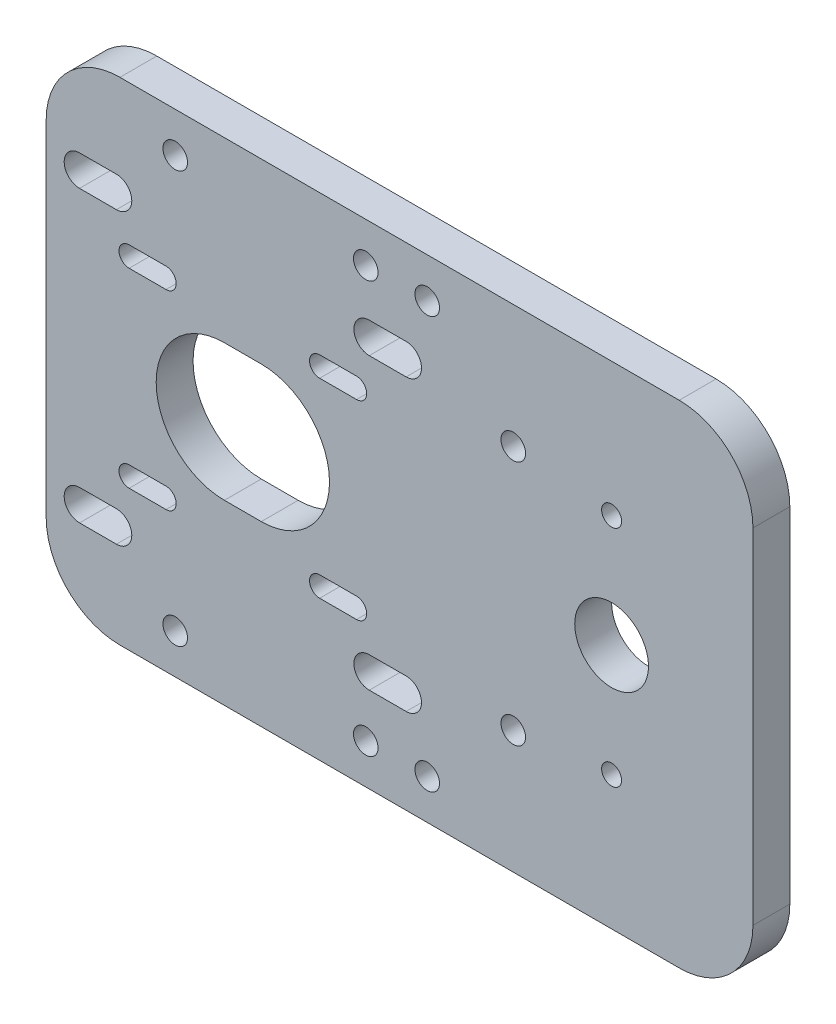
SolidWorks part; units mm, degrees
ref_plane "Alzado" through (0, 0, 0) normal (0, 0, 1) x (1, 0, 0)
ref_plane "Planta" through (0, 0, 0) normal (0, 1, 0) x (1, 0, 0)
ref_plane "Vista lateral" through (0, 0, 0) normal (1, 0, 0) x (0, 0, -1)
sketch "Croquis1" plane through (0, 0, 0) normal (0, 0, 1) x (1, 0, 0)
  line L1 (0, 0) -> (115, 0)
  line L2 (0, 0) -> (0, 80)
  line L3 (0, 80) -> (115, 80)
  line L4 (115, 0) -> (115, 80)
  dimension "D1" = 80
  dimension "D2" = 115
extrude "Saliente-Extruir1" add sketch "Croquis1" along normal blind 6
sketch "Croquis2" plane through (0, 0, 0) normal (0, 0, -1) x (-1, 0, 0)
  line L0 (0, 80) -> (0, 0) construction
  line L1 (0, 40) -> (-115, 40) construction
  line L4 (-115, 0) -> (-115, 80) construction
  line L7 (-29, 40) -> (-35, 40) construction
  line L10 (-29, 28.9) -> (-35, 28.9)
  line L19 (-29, 51.1) -> (-35, 51.1)
  line L20 (-13.5, 24.5) -> (-19.5, 24.5) construction
  line L21 (-13.5, 22.85) -> (-19.5, 22.85)
  line L22 (-13.5, 26.15) -> (-19.5, 26.15)
  line L23 (-44.5, 55.5) -> (-50.5, 55.5) construction
  line L24 (-44.5, 53.85) -> (-50.5, 53.85)
  line L25 (-44.5, 57.15) -> (-50.5, 57.15)
  line L26 (-44.5, 24.5) -> (-50.5, 24.5) construction
  line L27 (-44.5, 22.85) -> (-50.5, 22.85)
  line L28 (-44.5, 26.15) -> (-50.5, 26.15)
  line L29 (-13.5, 55.5) -> (-19.5, 55.5) construction
  line L30 (-13.5, 53.85) -> (-19.5, 53.85)
  line L31 (-13.5, 57.15) -> (-19.5, 57.15)
  line L32 (-92, 0) -> (-92, 80) construction
  line L33 (0, 0) -> (-115, 0) construction
  line L34 (-115, 80) -> (0, 80) construction
  line L35 (-61, 0) -> (-61, 80) construction
  line L36 (-52.57, 16.43) -> (-58.57, 16.43) construction
  line L37 (-52.57, 13.93) -> (-58.57, 13.93)
  line L38 (-52.57, 18.93) -> (-58.57, 18.93)
  line L39 (-5.43, 16.43) -> (-11.43, 16.43) construction
  line L40 (-5.43, 13.93) -> (-11.43, 13.93)
  line L41 (-5.43, 18.93) -> (-11.43, 18.93)
  line L42 (-52.57, 63.57) -> (-58.57, 63.57) construction
  line L43 (-52.57, 61.07) -> (-58.57, 61.07)
  line L44 (-52.57, 66.07) -> (-58.57, 66.07)
  line L45 (-5.43, 63.57) -> (-11.43, 63.57) construction
  line L46 (-5.43, 61.07) -> (-11.43, 61.07)
  line L47 (-5.43, 66.07) -> (-11.43, 66.07)
  circle A5 centre (-92, 40) radius 6
  circle A15 centre (-92, 21.75) radius 1.625
  circle A16 centre (-92, 58.25) radius 1.625
  arc A19 (-29, 28.9) -> (-29, 51.1) centre (-29, 40) ccw
  arc A20 (-35, 51.1) -> (-35, 28.9) centre (-35, 40) ccw
  arc A21 (-13.5, 22.85) -> (-13.5, 26.15) centre (-13.5, 24.5) ccw
  arc A22 (-19.5, 26.15) -> (-19.5, 22.85) centre (-19.5, 24.5) ccw
  arc A23 (-44.5, 53.85) -> (-44.5, 57.15) centre (-44.5, 55.5) ccw
  arc A24 (-50.5, 57.15) -> (-50.5, 53.85) centre (-50.5, 55.5) ccw
  arc A25 (-44.5, 22.85) -> (-44.5, 26.15) centre (-44.5, 24.5) ccw
  arc A26 (-50.5, 26.15) -> (-50.5, 22.85) centre (-50.5, 24.5) ccw
  arc A27 (-13.5, 53.85) -> (-13.5, 57.15) centre (-13.5, 55.5) ccw
  arc A28 (-19.5, 57.15) -> (-19.5, 53.85) centre (-19.5, 55.5) ccw
  arc A29 (-52.57, 13.93) -> (-52.57, 18.93) centre (-52.57, 16.43) ccw
  arc A30 (-58.57, 18.93) -> (-58.57, 13.93) centre (-58.57, 16.43) ccw
  arc A31 (-5.43, 13.93) -> (-5.43, 18.93) centre (-5.43, 16.43) ccw
  arc A32 (-11.43, 18.93) -> (-11.43, 13.93) centre (-11.43, 16.43) ccw
  arc A33 (-52.57, 61.07) -> (-52.57, 66.07) centre (-52.57, 63.57) ccw
  arc A34 (-58.57, 66.07) -> (-58.57, 61.07) centre (-58.57, 63.57) ccw
  arc A35 (-5.43, 61.07) -> (-5.43, 66.07) centre (-5.43, 63.57) ccw
  arc A36 (-11.43, 66.07) -> (-11.43, 61.07) centre (-11.43, 63.57) ccw
  circle A37 centre (-76, 20) radius 2
  circle A38 centre (-76, 60) radius 2
  point P6 (-32, 40)
  point P19 (-16.5, 24.5)
  point P28 (-47.5, 55.5)
  point P35 (-47.5, 24.5)
  point P41 (-55.57, 16.43)
  point P48 (-16.5, 55.5)
  point P63 (-8.43, 16.43)
  point P72 (-55.57, 63.57)
  point P79 (-8.43, 63.57)
  dimension "D2" = 6
  dimension "D3" = 11.1
  dimension "D4" = 3.3
  dimension "D5" = 6
  dimension "D6" = 12
  dimension "D13" = 3.25
  dimension "D14" = 3.25
  dimension "D29" = 2.5
  dimension "D32" = 2.5
  dimension "D34" = 2.5
  dimension "D36" = 2.5
  dimension "D45" = 4
  dimension "D46" = 4
  dimension "D7" = 15.5
  dimension "D8" = 15.5
  dimension "D9" = 3.3
  dimension "D10" = 6
  dimension "D11" = 23
  dimension "D12" = 40
  dimension "D15" = 18.25
  dimension "D16" = 18.25
  dimension "D17" = 3.3
  dimension "D18" = 6
  dimension "D19" = 3.3
  dimension "D20" = 6
  dimension "D21" = 15.5
  dimension "D22" = 15.5
  dimension "D23" = 15.5
  dimension "D24" = 15.5
  dimension "D25" = 15.5
  dimension "D26" = 15.5
  dimension "D27" = 60
  dimension "D28" = 26
  dimension "D30" = 6
  dimension "D31" = 6
  dimension "D33" = 6
  dimension "D35" = 6
  dimension "D37" = 23.57
  dimension "D38" = 23.57
  dimension "D39" = 23.57
  dimension "D40" = 23.57
  dimension "D41" = 23.57
  dimension "D42" = 23.57
  dimension "D43" = 23.57
  dimension "D44" = 23.57
  dimension "D47" = 20
  dimension "D48" = 39
  dimension "D49" = 39
  dimension "D50" = 20
extrude "Cortar-Extruir1" cut sketch "Croquis2" against normal through all
fillet "Redondeo1" radius 12 4 edges at (115, 0, 3) (115, 80, 3) (0, 0, 3) (0, 80, 3)
sketch "Croquis3" plane through (0, 0, 0) normal (0, 0, -1) x (-1, 0, 0)
  line L0 (-12, 0) -> (-103, 0) construction
  line L1 (0, 68) -> (0, 12) construction
  line L2 (-103, 80) -> (-12, 80) construction
  circle A0 centre (-21, 6.5) radius 2
  circle A1 centre (-62, 6.5) radius 2
  circle A2 centre (-62, 73.5) radius 2
  circle A3 centre (-21, 73.5) radius 2
  circle A4 centre (-52, 6.5) radius 2
  circle A5 centre (-52, 73.5) radius 2
  dimension "D1" = 4
  dimension "D2" = 4
  dimension "D3" = 4
  dimension "D4" = 4
  dimension "D13" = 4
  dimension "D14" = 4
  dimension "D5" = 6.5
  dimension "D6" = 6.5
  dimension "D7" = 21
  dimension "D8" = 62
  dimension "D9" = 6.5
  dimension "D10" = 6.5
  dimension "D11" = 21
  dimension "D12" = 62
  dimension "D15" = 6.5
  dimension "D16" = 6.5
  dimension "D17" = 52
  dimension "D18" = 52
extrude "Cortar-Extruir2" cut sketch "Croquis3" against normal through all
